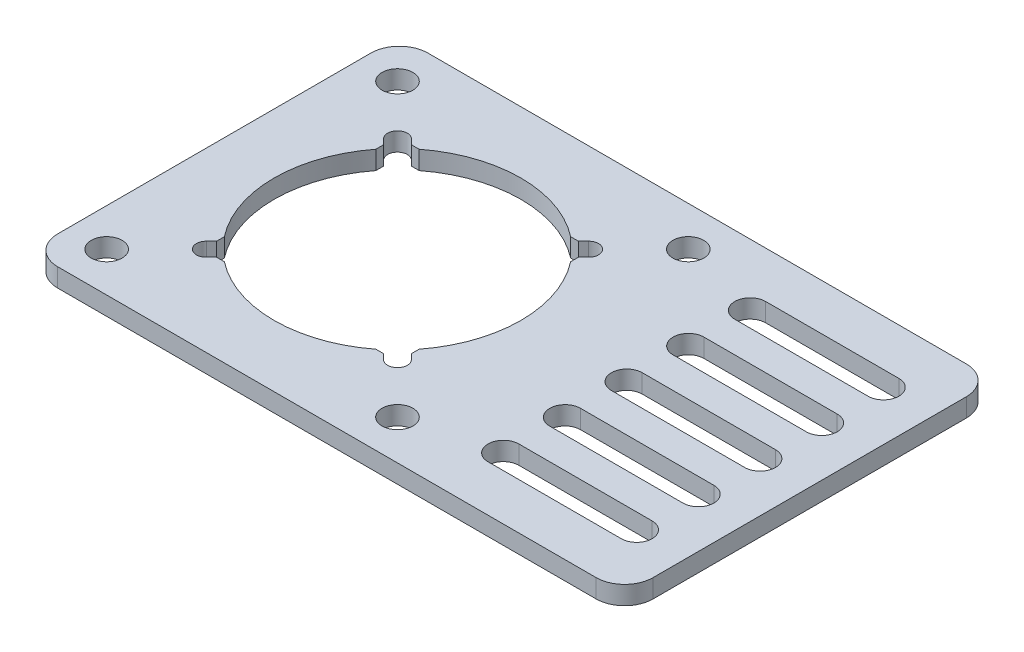
SolidWorks part; units mm, degrees
ref_plane "Front" through (0, 0, 0) normal (0, 0, 1) x (1, 0, 0)
ref_plane "Top" through (0, 0, 0) normal (0, 1, 0) x (1, 0, 0)
ref_plane "Right" through (0, 0, 0) normal (1, 0, 0) x (0, 0, -1)
sketch "Sketch2" plane through (0, 0, 0) normal (0, 1, 0) x (1, 0, 0)
  line L0 (-42.13, 6.43) -> (-42.13, 53.57) construction
  line L1 (-43.63, 60) -> (43.63, 60)
  line L2 (-48.25, 55.38) -> (-48.25, 4.62)
  line L3 (-43.63, 0) -> (43.63, 0)
  line L4 (48.25, 55.38) -> (48.25, 4.62)
  line L5 (-42.13, 53.57) -> (5.01, 53.57) construction
  line L6 (5.01, 53.57) -> (5.01, 6.43) construction
  line L7 (5.01, 6.43) -> (-42.13, 6.43) construction
  line L8 (-48.25, 30) -> (48.25, 30) construction
  line L9 (-18.56, 53.57) -> (-18.56, 30) construction
  line L10 (18.61, 50) -> (40.21, 50) construction
  line L11 (18.61, 52.5) -> (40.21, 52.5)
  line L12 (18.61, 47.5) -> (40.21, 47.5)
  line L13 (18.61, 10) -> (40.21, 10) construction
  line L14 (18.61, 7.5) -> (40.21, 7.5)
  line L15 (18.61, 12.5) -> (40.21, 12.5)
  line L16 (18.61, 30) -> (40.21, 30) construction
  line L17 (18.61, 32.5) -> (40.21, 32.5)
  line L18 (18.61, 27.5) -> (40.21, 27.5)
  line L19 (18.61, 40) -> (40.21, 40) construction
  line L20 (18.61, 42.5) -> (40.21, 42.5)
  line L21 (18.61, 37.5) -> (40.21, 37.5)
  line L22 (18.61, 20) -> (40.21, 20) construction
  line L23 (18.61, 17.5) -> (40.21, 17.5)
  line L24 (18.61, 22.5) -> (40.21, 22.5)
  line L25 (42.71, 0) -> (42.71, 60) construction
  line L26 (-34.0562, 14.5038) -> (-3.0638, 45.4962) construction
  line L27 (-34.0562, 45.4962) -> (-3.0638, 14.5038) construction
  line L28 (-5.0254, 45.7903) -> (-4.1916, 46.6241)
  line L29 (-2.7697, 43.5346) -> (-1.9359, 44.3684)
  line L30 (-5.0254, 45.7903) -> (-6.2854, 45.7903)
  line L31 (-2.7697, 43.5346) -> (-2.7697, 42.2746)
  line L32 (-32.0946, 45.7903) -> (-30.8346, 45.7903)
  line L33 (-34.3503, 43.5346) -> (-34.3503, 42.2746)
  line L34 (-34.3503, 43.5346) -> (-35.1841, 44.3684)
  line L35 (-32.0946, 45.7903) -> (-32.9284, 46.6241)
  line L36 (-5.0254, 14.2097) -> (-6.2854, 14.2097)
  line L37 (-5.0254, 14.2097) -> (-4.1916, 13.3759)
  line L38 (-2.7697, 16.4654) -> (-1.9359, 15.6316)
  line L39 (-2.7697, 16.4654) -> (-2.7697, 17.7254)
  line L40 (-32.0946, 14.2097) -> (-30.8346, 14.2097)
  line L41 (-32.0946, 14.2097) -> (-32.9284, 13.3759)
  line L42 (-34.3503, 16.4654) -> (-35.1841, 15.6316)
  line L43 (-34.3503, 16.4654) -> (-34.3503, 17.7254)
  arc A0 (-48.25, 4.62) -> (-43.63, 0) centre (-43.63, 4.62) ccw
  arc A1 (43.63, 0) -> (48.25, 4.62) centre (43.63, 4.62) ccw
  arc A2 (48.25, 55.38) -> (43.63, 60) centre (43.63, 55.38) ccw
  arc A3 (-43.63, 60) -> (-48.25, 55.38) centre (-43.63, 55.38) ccw
  circle A4 centre (-42.13, 6.43) radius 2.5
  circle A5 centre (-42.13, 53.57) radius 2.5
  circle A6 centre (5.01, 53.57) radius 2.5
  circle A7 centre (5.01, 6.43) radius 2.5
  arc A8 (-6.2854, 45.7903) -> (-30.8346, 45.7903) centre (-18.56, 30) ccw
  arc A9 (18.61, 52.5) -> (18.61, 47.5) centre (18.61, 50) ccw
  arc A10 (40.21, 47.5) -> (40.21, 52.5) centre (40.21, 50) ccw
  arc A11 (18.61, 7.5) -> (18.61, 12.5) centre (18.61, 10) cw
  arc A12 (40.21, 12.5) -> (40.21, 7.5) centre (40.21, 10) cw
  arc A13 (18.61, 32.5) -> (18.61, 27.5) centre (18.61, 30) ccw
  arc A14 (40.21, 27.5) -> (40.21, 32.5) centre (40.21, 30) ccw
  arc A15 (18.61, 42.5) -> (18.61, 37.5) centre (18.61, 40) ccw
  arc A16 (40.21, 37.5) -> (40.21, 42.5) centre (40.21, 40) ccw
  arc A17 (18.61, 17.5) -> (18.61, 22.5) centre (18.61, 20) cw
  arc A18 (40.21, 22.5) -> (40.21, 17.5) centre (40.21, 20) cw
  arc A19 (-32.9284, 46.6241) -> (-35.1841, 44.3684) centre (-34.0562, 45.4962) ccw
  arc A20 (-1.9359, 44.3684) -> (-4.1916, 46.6241) centre (-3.0638, 45.4962) ccw
  arc A21 (-35.1841, 15.6316) -> (-32.9284, 13.3759) centre (-34.0562, 14.5038) ccw
  arc A22 (-4.1916, 13.3759) -> (-1.9359, 15.6316) centre (-3.0638, 14.5038) ccw
  arc A23 (-34.3503, 42.2746) -> (-34.3503, 17.7254) centre (-18.56, 30) ccw
  arc A24 (-30.8346, 14.2097) -> (-6.2854, 14.2097) centre (-18.56, 30) ccw
  arc A25 (-2.7697, 17.7254) -> (-2.7697, 42.2746) centre (-18.56, 30) ccw
  point P23 (-42.13, 30)
  point P26 (-18.56, 53.57)
  point P30 (29.41, 50)
  point P37 (29.41, 10)
  point P44 (29.41, 30)
  point P51 (29.41, 40)
  point P58 (29.41, 20)
  point P67 (-18.56, 30)
  point P70 (-69.7607, 51.4198)
  dimension "D1" = 4.62
  dimension "D4" = 5
  dimension "D8" = 26.6
  dimension "D10" = 10
  dimension "D12" = 5.54
  dimension "D13" = 45
  dimension "D15" = 3.19
  dimension "D18" = 40
  dimension "D14" = 47.02
  dimension "D2" = 96.5
  dimension "D3" = 60
  dimension "D5" = 47.14
  dimension "D6" = 47.14
  dimension "D7" = 66.81
  dimension "D9" = 10
  dimension "D11" = 5
  dimension "D16" = 45
  dimension "D17" = 1.26
extrude "Boss-Extrude1" add sketch "Sketch2" along normal blind 3
